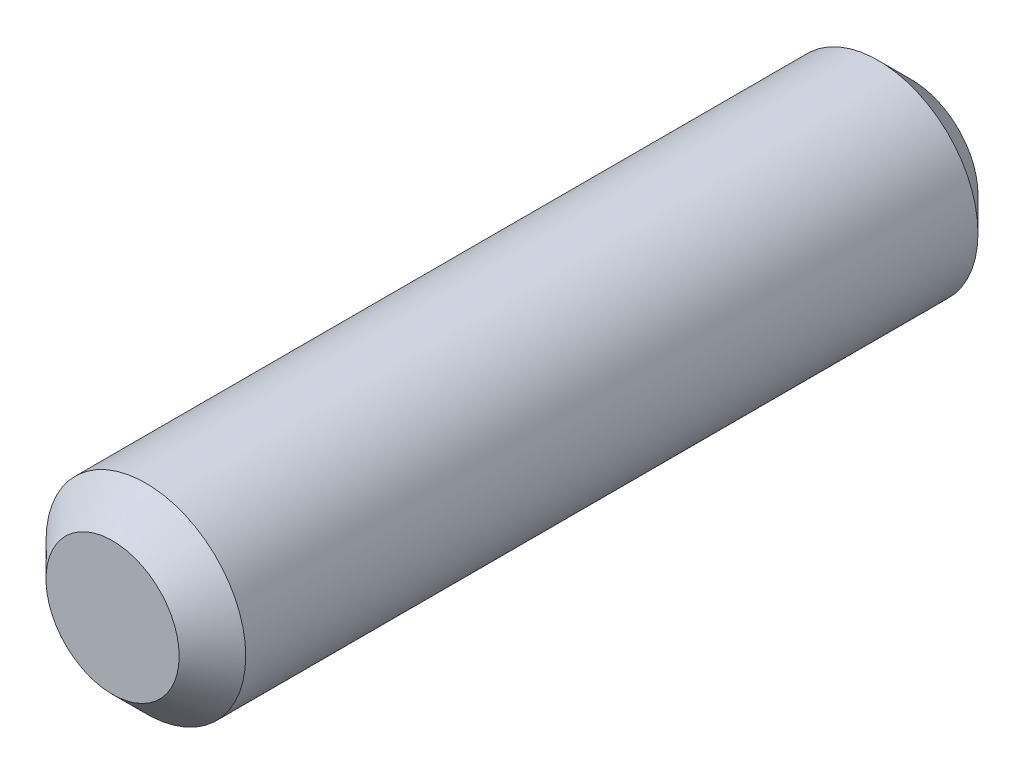
SolidWorks part; units mm, degrees
ref_plane "Front Plane" through (0, 0, 0) normal (0, 0, 1) x (1, 0, 0)
ref_plane "Top Plane" through (0, 0, 0) normal (0, 1, 0) x (1, 0, 0)
ref_plane "Right Plane" through (0, 0, 0) normal (1, 0, 0) x (0, 0, -1)
sketch "Sketch1" plane through (0, 0, 0) normal (0, 0, 1) x (1, 0, 0)
  circle A0 centre (0, 0) radius 1.5
  dimension "D1" = 3
extrude "Boss-Extrude1" add sketch "Sketch1" along normal blind 12
chamfer "Chamfer1" distance 0.5 angle 45 2 edges at (1.5, 0, 0) (1.5, 0, 12)
